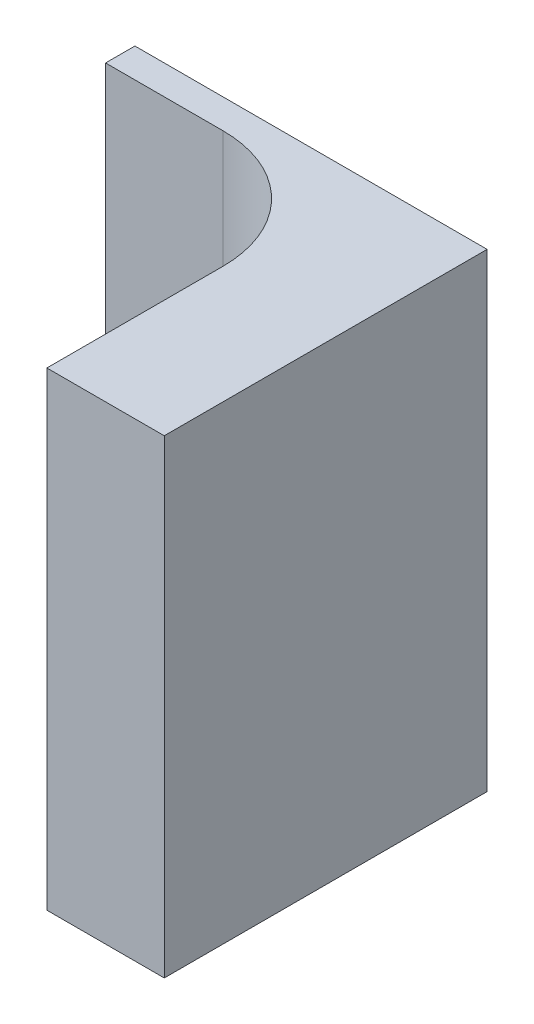
SolidWorks part; units mm, degrees
material "6061-T6 (SS)"
ref_plane "Front Plane" through (0, 0, 0) normal (0, 0, 1) x (1, 0, 0)
ref_plane "Top Plane" through (0, 0, 0) normal (0, 1, 0) x (1, 0, 0)
ref_plane "Right Plane" through (0, 0, 0) normal (1, 0, 0) x (0, 0, -1)
ref_plane "Plane1" through (0, 0, 15.875) normal (0, 0, 1) x (1, 0, 0)
sketch "Sketch1" plane through (0, 0, 15.875) normal (0, 0, 1) x (1, 0, 0)
  line L0 (0, -25.4) -> (0, 25.4) construction
  line L1 (0, 25.4) -> (-38.1, 25.4) construction
  line L2 (-38.1, 25.4) -> (-38.1, -25.4)
  line L3 (-38.1, -25.4) -> (-25.4, -25.4)
  line L5 (0, 25.4) -> (-38.1, 25.4)
  line L6 (-25.4, -25.4) -> (0, -25.4)
  line L7 (0, -25.4) -> (0, 25.4)
  point P2 (0, 0)
  dimension "D1" = 50.8
  dimension "D2" = 38.1
  dimension "D3" = 12.7
extrude "Boss-Extrude1" add sketch "Sketch1" along normal blind 3.175
ref_plane "Plane2" through (0, 0, 50.8) normal (0, 0, 1) x (1, 0, 0)
sketch "Sketch2" plane through (0, 0, 50.8) normal (0, 0, 1) x (1, 0, 0)
  line L0 (0, -25.4) -> (0, 25.4) construction
  line L1 (0, 25.4) -> (-12.7, 25.4)
  line L2 (-12.7, 25.4) -> (-12.7, -25.4)
  line L3 (-12.7, -25.4) -> (0, -25.4)
  line L4 (0, -25.4) -> (0, 25.4)
  point P2 (0, 0)
  dimension "D1" = 50.8
  dimension "D2" = 12.7
extrude "Boss-Extrude2" add sketch "Sketch2" against normal up to surface (31.75 mm away) up to face at (-19.05, 0, 19.05)
fillet "Fillet1" radius 12.7 1 edges at (-12.7, 0, 19.05)
